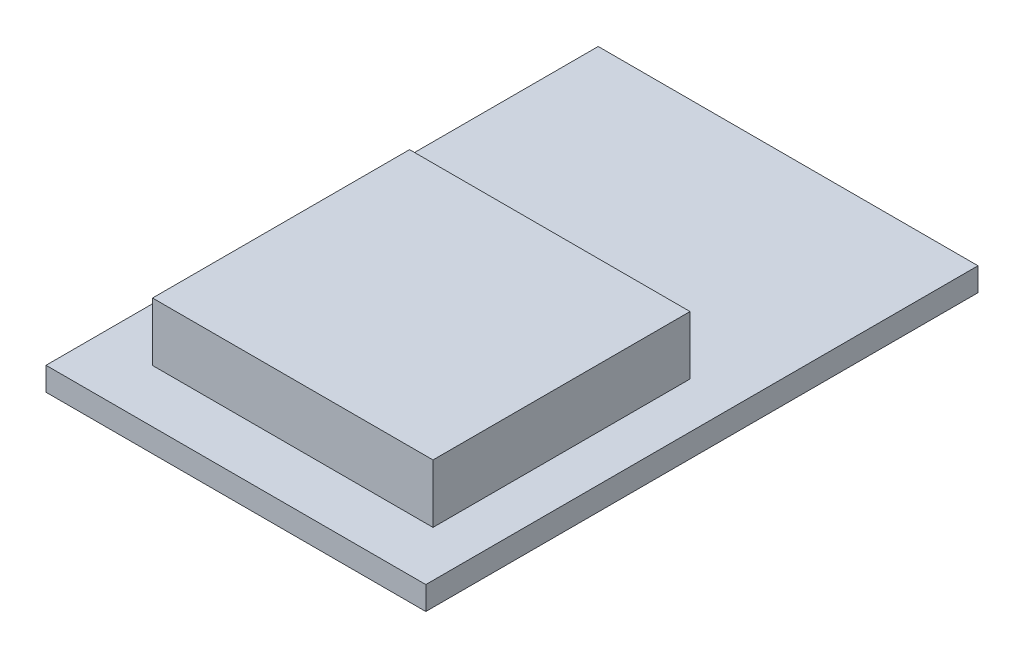
SolidWorks part; units mm, degrees
ref_plane "Front Plane" through (0, 0, 0) normal (0, 0, 1) x (1, 0, 0)
ref_plane "Top Plane" through (0, 0, 0) normal (0, 1, 0) x (1, 0, 0)
ref_plane "Right Plane" through (0, 0, 0) normal (1, 0, 0) x (0, 0, -1)
sketch "Sketch1" plane through (0, 0, 0) normal (0, 1, 0) x (1, 0, 0)
  line L1 (0, 0) -> (13, 0)
  line L2 (0, 0) -> (0, 18.9)
  line L3 (0, 18.9) -> (13, 18.9)
  line L4 (13, 0) -> (13, 18.9)
  line L5 (0, 0) -> (13, 18.9) construction
  line L6 (0, 18.9) -> (13, 0) construction
  point P4 (6.5, 9.45)
  dimension "D1" = 13
  dimension "D2" = 18.9
extrude "Boss-Extrude1" add sketch "Sketch1" along normal blind 0.8
sketch "Sketch2" plane through (0, 0.8, 0) normal (0, 1, 0) x (1, 0, 0)
  line L1 (1.8297, 10.6144) -> (11.4291, 10.6144)
  line L2 (1.8297, 10.6144) -> (1.8297, 1.817)
  line L3 (1.8297, 1.817) -> (11.4291, 1.817)
  line L4 (11.4291, 10.6144) -> (11.4291, 1.817)
  line L5 (1.8297, 10.6144) -> (11.4291, 1.817) construction
  line L6 (1.8297, 1.817) -> (11.4291, 10.6144) construction
  point P4 (6.6294, 6.2157)
extrude "Boss-Extrude2" add sketch "Sketch2" along normal blind 2
